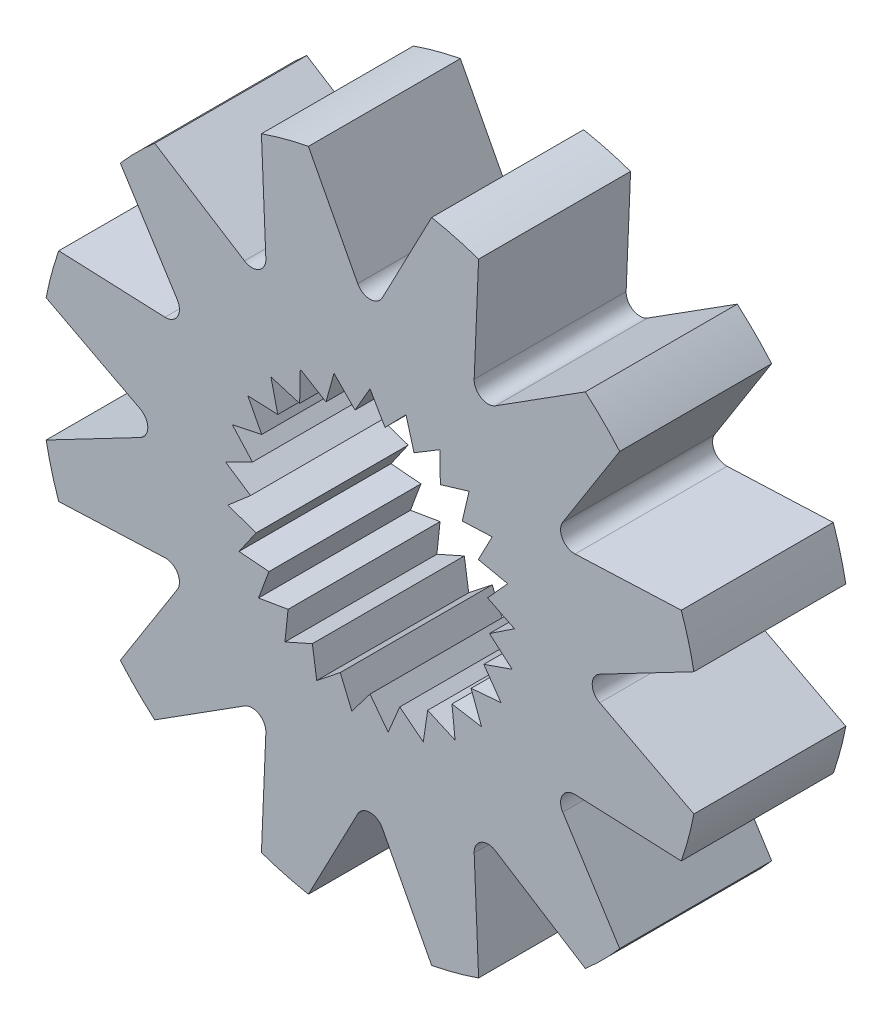
SolidWorks part; units mm, degrees
ref_plane "Front Plane" through (0, 0, 0) normal (0, 0, 1) x (1, 0, 0)
ref_plane "Top Plane" through (0, 0, 0) normal (0, 1, 0) x (1, 0, 0)
ref_plane "Right Plane" through (0, 0, 0) normal (1, 0, 0) x (0, 0, -1)
sketch "Sketch1" plane through (0, 0, 0) normal (0, 0, 1) x (1, 0, 0)
  line L0 (0, 3.048) -> (0, 0) construction
  line L1 (0, 3.048) -> (-0.3159, 2.5008)
  line L2 (0, 3.048) -> (0.3159, 2.5008)
  line L3 (-0.3159, 2.5008) -> (0.3159, 2.5008) construction
  line L4 (0.758, 2.9522) -> (0.3159, 2.5008)
  line L5 (0.758, 2.9522) -> (0.9279, 2.3437)
  line L6 (0.3159, 2.5008) -> (0.9279, 2.3437) construction
  line L7 (1.4684, 2.671) -> (0.9279, 2.3437)
  line L8 (1.4684, 2.671) -> (1.4816, 2.0393)
  line L9 (0.9279, 2.3437) -> (1.4816, 2.0393) construction
  line L10 (2.0865, 2.2219) -> (1.4816, 2.0393)
  line L11 (2.0865, 2.2219) -> (1.9422, 1.6067)
  line L12 (1.4816, 2.0393) -> (1.9422, 1.6067) construction
  line L13 (2.5735, 1.6332) -> (1.9422, 1.6067)
  line L14 (2.5735, 1.6332) -> (2.2808, 1.0733)
  line L15 (1.9422, 1.6067) -> (2.2808, 1.0733) construction
  line L16 (2.8988, 0.9419) -> (2.2808, 1.0733)
  line L17 (2.8988, 0.9419) -> (2.476, 0.4723)
  line L18 (2.2808, 1.0733) -> (2.476, 0.4723) construction
  line L19 (3.042, 0.1914) -> (2.476, 0.4723)
  line L20 (3.042, 0.1914) -> (2.5157, -0.1583)
  line L21 (2.476, 0.4723) -> (2.5157, -0.1583) construction
  line L22 (2.994, -0.5711) -> (2.5157, -0.1583)
  line L23 (2.994, -0.5711) -> (2.3973, -0.7789)
  line L24 (2.5157, -0.1583) -> (2.3973, -0.7789) construction
  line L25 (2.7579, -1.2978) -> (2.3973, -0.7789)
  line L26 (2.7579, -1.2978) -> (2.1283, -1.3506)
  line L27 (2.3973, -0.7789) -> (2.1283, -1.3506) construction
  line L28 (2.3485, -1.9429) -> (2.1283, -1.3506)
  line L29 (2.3485, -1.9429) -> (1.7255, -1.8375)
  line L30 (2.1283, -1.3506) -> (1.7255, -1.8375) construction
  line L31 (1.7916, -2.4659) -> (1.7255, -1.8375)
  line L32 (1.7916, -2.4659) -> (1.2143, -2.2089)
  line L33 (1.7255, -1.8375) -> (1.2143, -2.2089) construction
  line L34 (1.122, -2.834) -> (1.2143, -2.2089)
  line L35 (1.122, -2.834) -> (0.6269, -2.4415)
  line L36 (1.2143, -2.2089) -> (0.6269, -2.4415) construction
  line L37 (0.382, -3.024) -> (0.6269, -2.4415)
  line L38 (0.382, -3.024) -> (0, -2.5207)
  line L39 (0.6269, -2.4415) -> (0, -2.5207) construction
  line L40 (-0.382, -3.024) -> (0, -2.5207)
  line L41 (-0.382, -3.024) -> (-0.6269, -2.4415)
  line L42 (0, -2.5207) -> (-0.6269, -2.4415) construction
  line L43 (-1.122, -2.834) -> (-0.6269, -2.4415)
  line L44 (-1.122, -2.834) -> (-1.2143, -2.2089)
  line L45 (-0.6269, -2.4415) -> (-1.2143, -2.2089) construction
  line L46 (-1.7916, -2.4659) -> (-1.2143, -2.2089)
  line L47 (-1.7916, -2.4659) -> (-1.7255, -1.8375)
  line L48 (-1.2143, -2.2089) -> (-1.7255, -1.8375) construction
  line L49 (-2.3485, -1.9429) -> (-1.7255, -1.8375)
  line L50 (-2.3485, -1.9429) -> (-2.1283, -1.3506)
  line L51 (-1.7255, -1.8375) -> (-2.1283, -1.3506) construction
  line L52 (-2.7579, -1.2978) -> (-2.1283, -1.3506)
  line L53 (-2.7579, -1.2978) -> (-2.3973, -0.7789)
  line L54 (-2.1283, -1.3506) -> (-2.3973, -0.7789) construction
  line L55 (-2.994, -0.5711) -> (-2.3973, -0.7789)
  line L56 (-2.994, -0.5711) -> (-2.5157, -0.1583)
  line L57 (-2.3973, -0.7789) -> (-2.5157, -0.1583) construction
  line L58 (-3.042, 0.1914) -> (-2.5157, -0.1583)
  line L59 (-3.042, 0.1914) -> (-2.476, 0.4723)
  line L60 (-2.5157, -0.1583) -> (-2.476, 0.4723) construction
  line L61 (-2.8988, 0.9419) -> (-2.476, 0.4723)
  line L62 (-2.8988, 0.9419) -> (-2.2808, 1.0733)
  line L63 (-2.476, 0.4723) -> (-2.2808, 1.0733) construction
  line L64 (-2.5735, 1.6332) -> (-2.2808, 1.0733)
  line L65 (-2.5735, 1.6332) -> (-1.9422, 1.6067)
  line L66 (-2.2808, 1.0733) -> (-1.9422, 1.6067) construction
  line L67 (-2.0865, 2.2219) -> (-1.9422, 1.6067)
  line L68 (-2.0865, 2.2219) -> (-1.4816, 2.0393)
  line L69 (-1.9422, 1.6067) -> (-1.4816, 2.0393) construction
  line L70 (-1.4684, 2.671) -> (-1.4816, 2.0393)
  line L71 (-1.4684, 2.671) -> (-0.9279, 2.3437)
  line L72 (-1.4816, 2.0393) -> (-0.9279, 2.3437) construction
  line L73 (-0.758, 2.9522) -> (-0.9279, 2.3437)
  line L74 (-0.758, 2.9522) -> (-0.3159, 2.5008)
  line L75 (-0.9279, 2.3437) -> (-0.3159, 2.5008) construction
  circle A1 centre (0, 0) radius 6.9426
  point P0 (0, 2.5008)
  point P12 (0.6219, 2.4222)
  point P16 (1.2048, 2.1915)
  point P20 (1.7119, 1.823)
  point P24 (2.1115, 1.34)
  point P28 (2.3784, 0.7728)
  point P32 (2.4959, 0.157)
  point P36 (2.4565, -0.4686)
  point P40 (2.2628, -1.0648)
  point P44 (1.9269, -1.5941)
  point P48 (1.4699, -2.0232)
  point P52 (0.9206, -2.3252)
  point P56 (0.3134, -2.4811)
  point P60 (-0.3134, -2.4811)
  point P64 (-0.9206, -2.3252)
  point P68 (-1.4699, -2.0232)
  point P72 (-1.9269, -1.5941)
  point P76 (-2.2628, -1.0648)
  point P80 (-2.4565, -0.4686)
  point P84 (-2.4959, 0.157)
  point P88 (-2.3784, 0.7728)
  point P92 (-2.1115, 1.34)
  point P96 (-1.7119, 1.823)
  point P100 (-1.2048, 2.1915)
  point P104 (-0.6219, 2.4222)
  dimension "D1" = 25
  dimension "D3" = 13.8852
  dimension "D2" = 60
extrude "Boss-Extrude1" add sketch "Sketch1" along normal blind 3.2004
sketch "Sketch2" plane through (0, 0, 3.2004) normal (0, 0, 1) x (1, 0, 0)
  line L0 (-1.2972, 6.8203) -> (1.2972, 6.8203) construction
  line L1 (-1.2972, 6.8203) -> (-0.2598, 4.8367)
  line L2 (0, 0) -> (0.911, 6.8203) construction
  line L3 (0.2598, 4.8367) -> (1.2972, 6.8203)
  line L4 (-0.2598, 4.8367) -> (0.2598, 4.8367) construction
  line L5 (2.6434, 4.0588) -> (4.5336, 5.258)
  line L6 (-0.7785, 5.8285) -> (0.7785, 5.8285) construction
  line L7 (2.2868, 6.5552) -> (2.1933, 4.3187)
  line L8 (4.3187, 2.1933) -> (6.5552, 2.2868)
  line L9 (5.258, 4.5336) -> (4.0588, 2.6434)
  line L10 (4.8367, -0.2598) -> (6.8203, -1.2972)
  line L11 (6.8203, 1.2972) -> (4.8367, 0.2598)
  line L12 (4.0588, -2.6434) -> (5.258, -4.5336)
  line L13 (6.5552, -2.2868) -> (4.3187, -2.1933)
  line L14 (2.1933, -4.3187) -> (2.2868, -6.5552)
  line L15 (4.5336, -5.258) -> (2.6434, -4.0588)
  line L16 (-0.2598, -4.8367) -> (-1.2972, -6.8203)
  line L17 (1.2972, -6.8203) -> (0.2598, -4.8367)
  line L18 (-2.6434, -4.0588) -> (-4.5336, -5.258)
  line L19 (-2.2868, -6.5552) -> (-2.1933, -4.3187)
  line L20 (-4.3187, -2.1933) -> (-6.5552, -2.2868)
  line L21 (-5.258, -4.5336) -> (-4.0588, -2.6434)
  line L22 (-4.8367, 0.2598) -> (-6.8203, 1.2972)
  line L23 (-6.8203, -1.2972) -> (-4.8367, -0.2598)
  line L24 (-4.0588, 2.6434) -> (-5.258, 4.5336)
  line L25 (-6.5552, 2.2868) -> (-4.3187, 2.1933)
  line L26 (-2.1933, 4.3187) -> (-2.2868, 6.5552)
  line L27 (-4.5336, 5.258) -> (-2.6434, 4.0588)
  line L180 (0, 6.8203) -> (0, 0) construction
  arc A0 (0.2598, 4.8367) -> (-0.2598, 4.8367) centre (0, 4.9726) cw
  arc A1 (1.2972, 6.8203) -> (-1.2972, 6.8203) centre (0, 0) ccw
  arc A2 (2.6434, 4.0588) -> (2.1933, 4.3187) centre (2.4863, 4.3064) cw
  circle A3 centre (0, 0) radius 6.9426 construction
  arc A4 (4.5336, 5.258) -> (2.2868, 6.5552) centre (0, 0) ccw
  arc A5 (4.3187, 2.1933) -> (4.0588, 2.6434) centre (4.3064, 2.4863) cw
  arc A6 (6.5552, 2.2868) -> (5.258, 4.5336) centre (0, 0) ccw
  arc A7 (4.8367, -0.2598) -> (4.8367, 0.2598) centre (4.9726, 0) cw
  arc A8 (6.8203, -1.2972) -> (6.8203, 1.2972) centre (0, 0) ccw
  arc A9 (4.0588, -2.6434) -> (4.3187, -2.1933) centre (4.3064, -2.4863) cw
  arc A10 (5.258, -4.5336) -> (6.5552, -2.2868) centre (0, 0) ccw
  arc A11 (2.1933, -4.3187) -> (2.6434, -4.0588) centre (2.4863, -4.3064) cw
  arc A12 (2.2868, -6.5552) -> (4.5336, -5.258) centre (0, 0) ccw
  arc A13 (-0.2598, -4.8367) -> (0.2598, -4.8367) centre (0, -4.9726) cw
  arc A14 (-1.2972, -6.8203) -> (1.2972, -6.8203) centre (0, 0) ccw
  arc A15 (-2.6434, -4.0588) -> (-2.1933, -4.3187) centre (-2.4863, -4.3064) cw
  arc A16 (-4.5336, -5.258) -> (-2.2868, -6.5552) centre (0, 0) ccw
  arc A17 (-4.3187, -2.1933) -> (-4.0588, -2.6434) centre (-4.3064, -2.4863) cw
  arc A18 (-6.5552, -2.2868) -> (-5.258, -4.5336) centre (0, 0) ccw
  arc A19 (-4.8367, 0.2598) -> (-4.8367, -0.2598) centre (-4.9726, 0) cw
  arc A20 (-6.8203, 1.2972) -> (-6.8203, -1.2972) centre (0, 0) ccw
  arc A21 (-4.0588, 2.6434) -> (-4.3187, 2.1933) centre (-4.3064, 2.4863) cw
  arc A22 (-5.258, 4.5336) -> (-6.5552, 2.2868) centre (0, 0) ccw
  arc A23 (-2.1933, 4.3187) -> (-2.6434, 4.0588) centre (-2.4863, 4.3064) cw
  arc A24 (-2.2868, 6.5552) -> (-4.5336, 5.258) centre (0, 0) ccw
  point P1 (0, 5.8285)
  point P92 (0, 0)
  point P132 (0, 0)
  point P212 (0, 0)
  dimension "D1" = 0.9918
  dimension "D2" = 20
  dimension "D3" = 12
  dimension "D5" = 1.557
extrude "Cut-Extrude1" cut sketch "Sketch2" against normal up to surface (3.2004 mm away) up to face at (6.9426, 0, 0)
sketch "Sketch3" plane through (0, 0, 3.2004) normal (0, 0, 1) x (1, 0, 0)
  circle A0 centre (0, 0) radius 5.9508 construction
  circle A1 centre (0, 0) radius 6.9426 construction
  dimension "D1" = 11.9016
